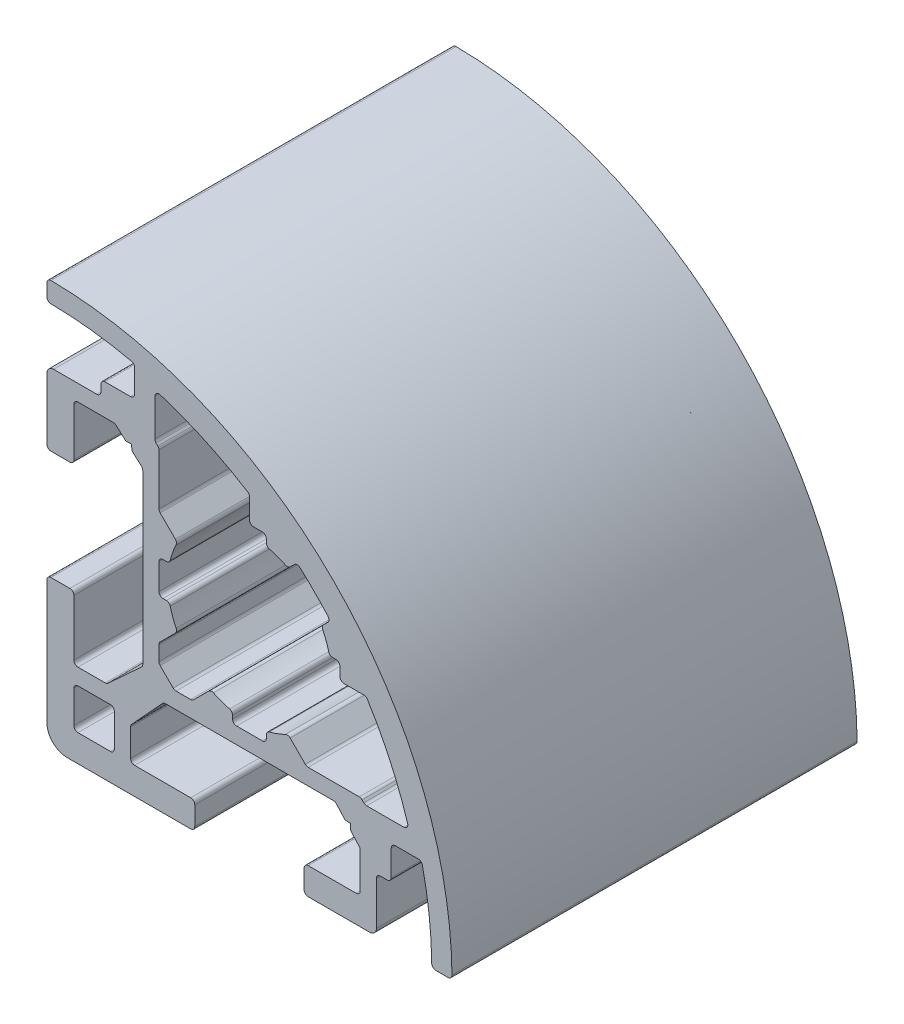
SolidWorks part; units mm, degrees
ref_plane "Plano frontal" through (0, 0, 0) normal (0, 0, 1) x (1, 0, 0)
ref_plane "Plano superior" through (0, 0, 0) normal (0, 1, 0) x (1, 0, 0)
ref_plane "Plano direito" through (0, 0, 0) normal (1, 0, 0) x (0, 0, -1)
ref_plane "Plano1" through (0, 0, 0) normal (0, 0, -1) x (-1, 0, 0)
sketch "Esboço1" plane through (0, 0, 0) normal (0, 0, -1) x (-1, 0, 0)
  line L0 (12.7, -13) -> (10.3, -13)
  line L1 (10, -12.7) -> (10, -10.3)
  line L2 (10.3, -10) -> (12.7, -10)
  line L3 (13, -10.3) -> (13, -12.7)
  line L4 (-0.95, 6.7) -> (-0.3, 6.7)
  line L5 (0, 7) -> (0, 8.4776)
  line L6 (7, 11.4273) -> (7, 8.6799)
  line L7 (6.9121, 8.4678) -> (6.7879, 8.3435)
  line L8 (6.7, 8.1314) -> (6.7, 4.3494)
  line L9 (6.6121, 4.1372) -> (5.4871, 3.0123)
  line L10 (6.1579, 1.25) -> (6.4, 1.25)
  line L11 (6.7, 0.95) -> (6.7, -0.95)
  line L12 (6.4, -1.25) -> (6.1579, -1.25)
  line L13 (5.4871, -3.0123) -> (6.6121, -4.1372)
  line L14 (6.7, -4.3494) -> (6.7, -5.4396)
  line L15 (6.6121, -5.6517) -> (5.6517, -6.6121)
  line L16 (5.4395, -6.7) -> (4.3494, -6.7)
  line L17 (4.1373, -6.6121) -> (3.0123, -5.4871)
  line L18 (1.25, -6.1579) -> (1.25, -6.4)
  line L19 (0.95, -6.7) -> (-0.95, -6.7)
  line L20 (-1.25, -6.4) -> (-1.25, -6.1579)
  line L21 (-3.0123, -5.4871) -> (-4.1373, -6.6121)
  line L22 (-4.3494, -6.7) -> (-8.1314, -6.7)
  line L23 (-8.3435, -6.7879) -> (-8.4678, -6.9121)
  line L24 (-8.6799, -7) -> (-11.4273, -7)
  line L25 (-8.4777, 0) -> (-7, 0)
  line L26 (-6.7, 0.3) -> (-6.7, 0.95)
  line L27 (-6.4, 1.25) -> (-6.1579, 1.25)
  line L28 (-5.4871, 3.0123) -> (-5.7974, 3.3226)
  line L29 (-3.3226, 5.7974) -> (-3.0123, 5.4871)
  line L30 (-1.25, 6.1579) -> (-1.25, 6.4)
  line L31 (7.9882, 6.432) -> (8.7045, 7.072)
  line L32 (8.7045, 7.072) -> (8.7283, 7.4958)
  line L33 (8.7283, 7.4958) -> (9.1516, 7.472)
  line L34 (9.1516, 7.472) -> (9.8678, 8.112)
  line L35 (10.08, 8.1999) -> (12.7001, 8.1998)
  line L36 (13.0001, 7.8998) -> (13, 4.3499)
  line L37 (13.3, 4.0499) -> (14.7, 4.0498)
  line L38 (15, 4.3498) -> (15, 8.8999)
  line L39 (14.5, 9.3999) -> (11.3, 9.3999)
  line L40 (11, 9.6999) -> (11, 10.1999)
  line L41 (10.7, 10.4999) -> (8.8, 10.4999)
  line L42 (8.5, 10.7999) -> (8.5, 12.51)
  line L43 (15, 13.7984) -> (15, 14.6985)
  line L44 (-14.6985, -15) -> (-13.7984, -15)
  line L45 (-12.5105, -8.5) -> (-10.8005, -8.5)
  line L46 (-10.5005, -8.8) -> (-10.5005, -10.7)
  line L47 (-10.2005, -11) -> (-9.7004, -11)
  line L48 (-9.4004, -11.3) -> (-9.4004, -14.5)
  line L49 (-8.9004, -15) -> (-4.3505, -15)
  line L50 (-4.0505, -14.7) -> (-4.0504, -13.3)
  line L51 (-4.3504, -13) -> (-7.9005, -12.9999)
  line L52 (-8.2005, -12.6999) -> (-8.2004, -10.0799)
  line L53 (-8.1126, -9.8677) -> (-7.4725, -9.1515)
  line L54 (-7.4725, -9.1515) -> (-7.4963, -8.728)
  line L55 (-7.4963, -8.728) -> (-7.0727, -8.7042)
  line L56 (-7.0727, -8.7042) -> (-6.4326, -7.988)
  line L57 (-6.2205, -7.9001) -> (6.2197, -7.9001)
  line L58 (6.4318, -7.988) -> (8.7117, -10.4679)
  line L59 (8.7996, -10.6801) -> (8.7996, -12.7001)
  line L60 (8.4996, -13.0001) -> (4.3496, -13.0001)
  line L61 (4.0496, -13.3001) -> (4.0496, -14.7)
  line L62 (4.3496, -15) -> (13.5, -15)
  line L63 (15, -13.5) -> (15, -4.3503)
  line L64 (14.7, -4.0503) -> (13.2999, -4.0503)
  line L65 (12.9999, -4.3503) -> (12.9999, -8.5003)
  line L66 (12.6999, -8.8003) -> (10.6798, -8.8003)
  line L67 (10.4677, -8.7124) -> (7.9878, -6.4325)
  line L68 (7.9003, -6.2203) -> (7.9003, 6.2198)
  arc A0 (10.3, -13) -> (10, -12.7) centre (10.3, -12.7) cw
  arc A1 (10, -10.3) -> (10.3, -10) centre (10.3, -10.3) cw
  arc A2 (12.7, -10) -> (13, -10.3) centre (12.7, -10.3) cw
  arc A3 (13, -12.7) -> (12.7, -13) centre (12.7, -12.7) cw
  arc A4 (-0.3, 6.7) -> (0, 7) centre (-0.3, 7) ccw
  arc A5 (0, 8.4776) -> (0.1408, 8.7319) centre (0.3, 8.4776) cw
  arc A6 (0.1408, 8.7319) -> (6.6101, 11.7135) centre (15, -15) cw
  arc A7 (6.6101, 11.7135) -> (7, 11.4273) centre (6.7, 11.4273) cw
  arc A8 (7, 8.6799) -> (6.9121, 8.4678) centre (6.7, 8.6799) cw
  arc A9 (6.7879, 8.3435) -> (6.7, 8.1314) centre (7, 8.1314) ccw
  arc A10 (6.7, 4.3494) -> (6.6121, 4.1372) centre (6.4, 4.3494) cw
  arc A11 (5.4871, 3.0123) -> (5.43, 2.6678) centre (5.6993, 2.8001) ccw
  arc A12 (5.43, 2.6678) -> (5.867, 1.4768) centre (0, 0) cw
  arc A13 (5.867, 1.4768) -> (6.1579, 1.25) centre (6.1579, 1.55) ccw
  arc A14 (6.4, 1.25) -> (6.7, 0.95) centre (6.4, 0.95) cw
  arc A15 (6.7, -0.95) -> (6.4, -1.25) centre (6.4, -0.95) cw
  arc A16 (6.1579, -1.25) -> (5.867, -1.4768) centre (6.1579, -1.55) ccw
  arc A17 (5.867, -1.4768) -> (5.43, -2.6678) centre (0, 0) cw
  arc A18 (5.43, -2.6678) -> (5.4871, -3.0123) centre (5.6993, -2.8001) ccw
  arc A19 (6.6121, -4.1372) -> (6.7, -4.3494) centre (6.4, -4.3494) cw
  arc A20 (6.7, -5.4396) -> (6.6121, -5.6517) centre (6.4, -5.4396) cw
  arc A21 (5.6517, -6.6121) -> (5.4395, -6.7) centre (5.4395, -6.4) cw
  arc A22 (4.3494, -6.7) -> (4.1373, -6.6121) centre (4.3494, -6.4) cw
  arc A23 (3.0123, -5.4871) -> (2.6678, -5.43) centre (2.8001, -5.6993) ccw
  arc A24 (2.6678, -5.43) -> (1.4768, -5.867) centre (0, 0) cw
  arc A25 (1.4768, -5.867) -> (1.25, -6.1579) centre (1.55, -6.1579) ccw
  arc A26 (1.25, -6.4) -> (0.95, -6.7) centre (0.95, -6.4) cw
  arc A27 (-0.95, -6.7) -> (-1.25, -6.4) centre (-0.95, -6.4) cw
  arc A28 (-1.25, -6.1579) -> (-1.4768, -5.867) centre (-1.55, -6.1579) ccw
  arc A29 (-1.4768, -5.867) -> (-2.6678, -5.43) centre (0, 0) cw
  arc A30 (-2.6678, -5.43) -> (-3.0123, -5.4871) centre (-2.8001, -5.6993) ccw
  arc A31 (-4.1373, -6.6121) -> (-4.3494, -6.7) centre (-4.3494, -6.4) cw
  arc A32 (-8.1314, -6.7) -> (-8.3435, -6.7879) centre (-8.1314, -7) ccw
  arc A33 (-8.4678, -6.9121) -> (-8.6799, -7) centre (-8.6799, -6.7) cw
  arc A34 (-11.4273, -7) -> (-11.7135, -6.6101) centre (-11.4273, -6.7) cw
  arc A35 (-11.7135, -6.6101) -> (-8.7319, -0.1408) centre (15, -15) cw
  arc A36 (-8.7319, -0.1408) -> (-8.4777, 0) centre (-8.4777, -0.3) cw
  arc A37 (-7, 0) -> (-6.7, 0.3) centre (-7, 0.3) ccw
  arc A38 (-6.7, 0.95) -> (-6.4, 1.25) centre (-6.4, 0.95) cw
  arc A39 (-6.1579, 1.25) -> (-5.867, 1.4768) centre (-6.1579, 1.55) ccw
  arc A40 (-5.867, 1.4768) -> (-5.43, 2.6678) centre (0, 0) cw
  arc A41 (-5.43, 2.6678) -> (-5.4871, 3.0123) centre (-5.6993, 2.8001) ccw
  arc A42 (-5.7974, 3.3226) -> (-5.8083, 3.7354) centre (-5.5853, 3.5347) cw
  arc A43 (-5.8083, 3.7354) -> (-3.7354, 5.8083) centre (15, -15) cw
  arc A44 (-3.7354, 5.8083) -> (-3.3226, 5.7974) centre (-3.5347, 5.5853) cw
  arc A45 (-3.0123, 5.4871) -> (-2.6678, 5.43) centre (-2.8001, 5.6993) ccw
  arc A46 (-2.6678, 5.43) -> (-1.4768, 5.867) centre (0, 0) cw
  arc A47 (-1.4768, 5.867) -> (-1.25, 6.1579) centre (-1.55, 6.1579) ccw
  arc A48 (-1.25, 6.4) -> (-0.95, 6.7) centre (-0.95, 6.4) cw
  arc A49 (9.8678, 8.112) -> (10.08, 8.1999) centre (10.08, 7.8999) cw
  arc A50 (12.7001, 8.1998) -> (13.0001, 7.8998) centre (12.7001, 7.8998) cw
  arc A51 (13, 4.3499) -> (13.3, 4.0499) centre (13.3, 4.3499) ccw
  arc A52 (14.7, 4.0498) -> (15, 4.3498) centre (14.7, 4.3498) ccw
  arc A53 (15, 8.8999) -> (14.5, 9.3999) centre (14.5, 8.8999) ccw
  arc A54 (11.3, 9.3999) -> (11, 9.6999) centre (11.3, 9.6999) cw
  arc A55 (11, 10.1999) -> (10.7, 10.4999) centre (10.7, 10.1999) ccw
  arc A56 (8.8, 10.4999) -> (8.5, 10.7999) centre (8.8, 10.7999) cw
  arc A57 (8.5, 12.51) -> (8.734, 12.8026) centre (8.8, 12.51) cw
  arc A58 (8.734, 12.8026) -> (14.7031, 13.4984) centre (15, -15) cw
  arc A59 (14.7031, 13.4984) -> (15, 13.7984) centre (14.7, 13.7984) ccw
  arc A60 (15, 14.6985) -> (14.697, 14.9985) centre (14.7, 14.6985) ccw
  arc A61 (14.697, 14.9985) -> (-14.9985, -14.697) centre (15, -15) ccw
  arc A62 (-14.9985, -14.697) -> (-14.6985, -15) centre (-14.6985, -14.7) ccw
  arc A63 (-13.7984, -15) -> (-13.4985, -14.7031) centre (-13.7984, -14.7) ccw
  arc A64 (-13.4985, -14.7031) -> (-12.8027, -8.734) centre (15, -15) cw
  arc A65 (-12.8027, -8.734) -> (-12.5105, -8.5) centre (-12.51, -8.8) cw
  arc A66 (-10.8005, -8.5) -> (-10.5005, -8.8) centre (-10.8005, -8.8) cw
  arc A67 (-10.5005, -10.7) -> (-10.2005, -11) centre (-10.2005, -10.7) ccw
  arc A68 (-9.7004, -11) -> (-9.4004, -11.3) centre (-9.7004, -11.3) cw
  arc A69 (-9.4004, -14.5) -> (-8.9004, -15) centre (-8.9004, -14.5) ccw
  arc A70 (-4.3505, -15) -> (-4.0505, -14.7) centre (-4.3505, -14.7) ccw
  arc A71 (-4.0504, -13.3) -> (-4.3504, -13) centre (-4.3504, -13.3) ccw
  arc A72 (-7.9005, -12.9999) -> (-8.2005, -12.6999) centre (-7.9005, -12.6999) cw
  arc A73 (-8.2004, -10.0799) -> (-8.1126, -9.8677) centre (-7.9004, -10.0799) cw
  arc A74 (-6.4326, -7.988) -> (-6.2205, -7.9001) centre (-6.2205, -8.2001) cw
  arc A75 (6.2197, -7.9001) -> (6.4318, -7.988) centre (6.2197, -8.2001) cw
  arc A76 (8.7117, -10.4679) -> (8.7996, -10.6801) centre (8.4996, -10.6801) cw
  arc A77 (8.7996, -12.7001) -> (8.4996, -13.0001) centre (8.4996, -12.7001) cw
  arc A78 (4.3496, -13.0001) -> (4.0496, -13.3001) centre (4.3496, -13.3001) ccw
  arc A79 (4.0496, -14.7) -> (4.3496, -15) centre (4.3496, -14.7) ccw
  arc A80 (13.5, -15) -> (15, -13.5) centre (13.5, -13.5) ccw
  arc A81 (15, -4.3503) -> (14.7, -4.0503) centre (14.7, -4.3503) ccw
  arc A82 (13.2999, -4.0503) -> (12.9999, -4.3503) centre (13.2999, -4.3503) ccw
  arc A83 (12.9999, -8.5003) -> (12.6999, -8.8003) centre (12.6999, -8.5003) cw
  arc A84 (10.6798, -8.8003) -> (10.4677, -8.7124) centre (10.6798, -8.5003) cw
  arc A85 (7.9878, -6.4325) -> (7.9003, -6.2203) centre (8.2003, -6.2208) cw
  arc A86 (7.9003, 6.2198) -> (7.9882, 6.432) centre (8.2003, 6.2198) cw
  dimension "D1" = 1.5
  dimension "D2" = 30
extrude "Ressalto-extrusão1" add sketch "Esboço1" against normal blind 30
sketch "Esboço2" plane through (0, 0, 0) normal (0, 0, -1) x (-1, 0, 0)
  line L3 (15, -13.5) -> (15, -4.3503) construction
  line L7 (15, 15) -> (-15, 15) construction
  line L8 (15, 15) -> (15, -15) construction
  line L9 (15, -15) -> (-15, -15) construction
  line L10 (-15, 15) -> (-15, -15) construction
  line L11 (15, 15) -> (-15, -15) construction
  line L12 (15, -15) -> (-15, 15) construction
  line L13 (4.3496, -15) -> (13.5, -15) construction
  point P0 (0, 0)
  point P9 (0, 0)
  dimension "D1" = 30
  dimension "D2" = 30
